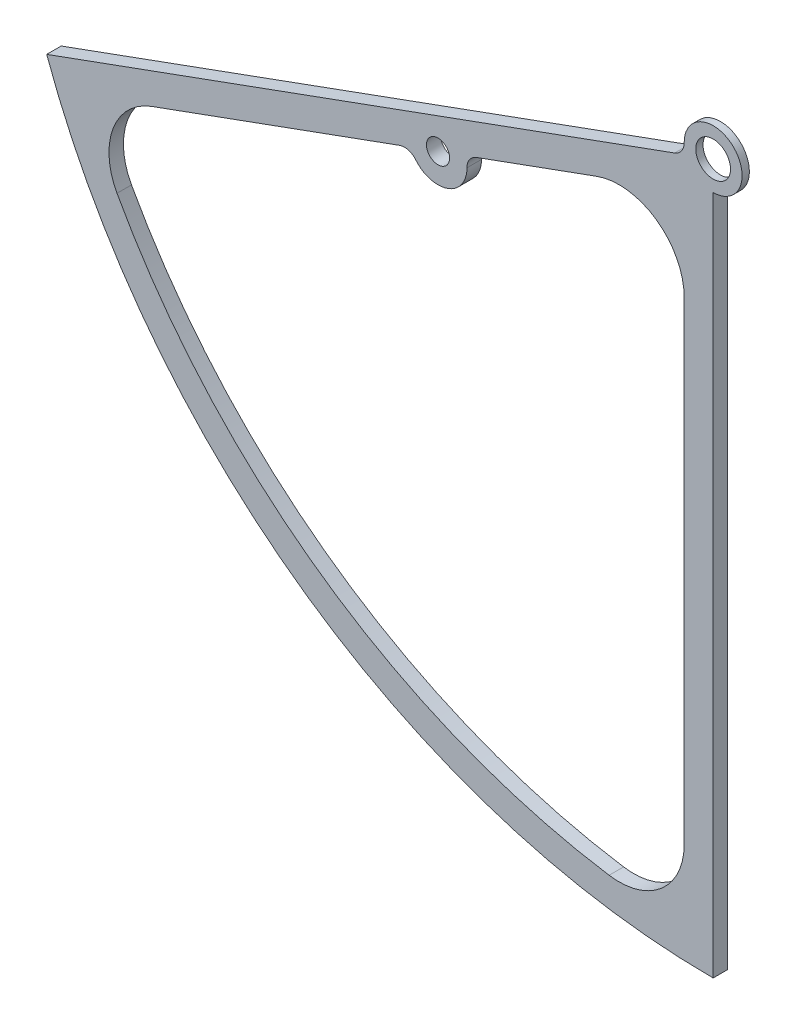
SolidWorks part; units mm, degrees
ref_plane "Płaszczyzna przednia" through (0, 0, 0) normal (0, 0, 1) x (1, 0, 0)
ref_plane "Płaszczyzna górna" through (0, 0, 0) normal (0, 1, 0) x (1, 0, 0)
ref_plane "Płaszczyzna prawa" through (0, 0, 0) normal (1, 0, 0) x (0, 0, -1)
sketch "Szkic1" plane through (0, 0, 0) normal (0, 0, 1) x (1, 0, 0)
  line L0 (0, -20) -> (0, -490)
  line L1 (-18.7939, -6.8404) -> (-460.4494, -167.5899)
  line L2 (-20, -28.563) -> (-20, -469.5743)
  line L3 (-20, -28.563) -> (-171.3011, -83.6321)
  line L4 (-208.8888, -97.3129) -> (-434.4151, -179.3977)
  line L5 (-20, -28.563) -> (-434.4151, -179.3977) construction
  arc A0 (-460.4494, -167.5899) -> (0, -490) centre (0, 0) ccw
  circle A1 centre (0, 0) radius 12
  arc A2 (0, -20) -> (-18.7939, -6.8404) centre (0, 0) ccw
  arc A3 (-434.4151, -179.3977) -> (-20, -469.5743) centre (0, 0) ccw
  arc A4 (-20, -28.563) -> (-20, -28.563) centre (-20, -28.563) ccw
  circle A5 centre (-190.095, -90.4725) radius 8
  arc A6 (-208.8888, -97.3129) -> (-171.3011, -83.6321) centre (-190.095, -90.4725) ccw
  dimension "D2" = 490
  dimension "D3" = 24
  dimension "D4" = 20
  dimension "D7" = 20
  dimension "D8" = 260
  dimension "D9" = 16
  dimension "D10" = 20
  dimension "D1" = 70
  dimension "D5" = 470
  dimension "D6" = 470
extrude "Dodanie-wyciągnięcie1" add sketch "Szkic1" along normal blind 10
sketch "Szkic2" plane through (0, 0, 0) normal (0, 0, -1) x (-1, 0, 0)
  circle A0 centre (0, 0) radius 20
  dimension "D1" = 40
extrude "Wytnij-wyciągnięcie1" cut sketch "Szkic2" against normal blind 5
fillet "Zaokrąglenie1" radius 45 3 edges at (-20, -469.5743, 5) (-20, -28.563, 5) (-434.4151, -179.3977, 5)
fillet "Zaokrąglenie2" radius 10 3 edges at (-18.7939, -6.8404, 7.5) (-171.3011, -83.6321, 5) (-208.8888, -97.3129, 5)
